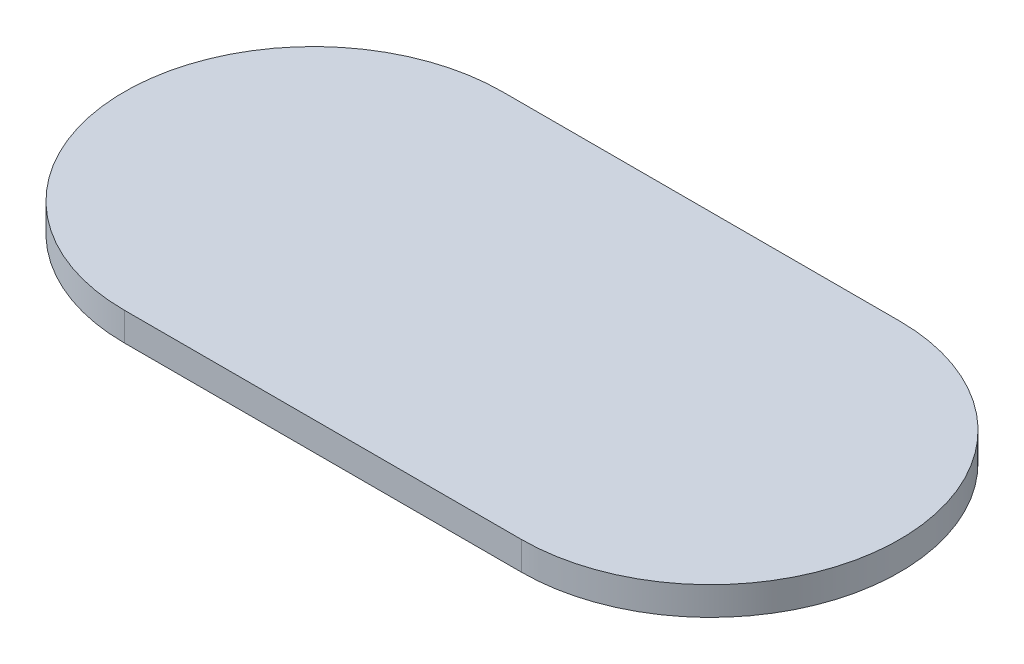
SolidWorks part; units mm, degrees
ref_plane "Front Plane" through (0, 0, 0) normal (0, 0, 1) x (1, 0, 0)
ref_plane "Top Plane" through (0, 0, 0) normal (0, 1, 0) x (1, 0, 0)
ref_plane "Right Plane" through (0, 0, 0) normal (1, 0, 0) x (0, 0, -1)
sketch "Sketch1" plane through (0, 0, 0) normal (0, 1, 0) x (1, 0, 0)
  line L1 (-26.67, -25.4) -> (26.67, -25.4)
  line L3 (-26.67, 25.4) -> (26.67, 25.4)
  line L5 (-26.67, -25.4) -> (26.67, 25.4) construction
  line L6 (-26.67, 25.4) -> (26.67, -25.4) construction
  arc A0 (-26.67, 25.4) -> (-26.67, -25.4) centre (-26.67, 0) ccw
  arc A1 (26.67, 25.4) -> (26.67, -25.4) centre (26.67, 0) cw
  point P0 (0, 0)
  point P8 (-52.07, 0)
  point P9 (52.07, 0)
  dimension "D1" = 50.8
  dimension "D2" = 104.14
extrude "Boss-Extrude1" add sketch "Sketch1" along normal blind 3.81
